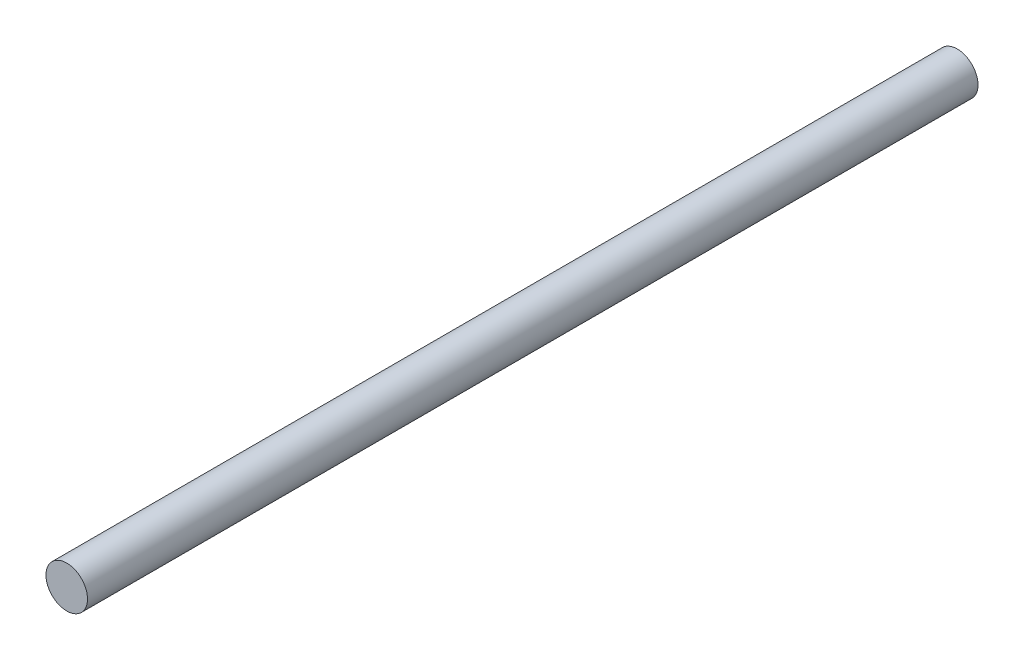
SolidWorks part; units mm, degrees
ref_plane "Front Plane" through (0, 0, 0) normal (0, 0, 1) x (1, 0, 0)
ref_plane "Top Plane" through (0, 0, 0) normal (0, 1, 0) x (1, 0, 0)
ref_plane "Right Plane" through (0, 0, 0) normal (1, 0, 0) x (0, 0, -1)
sketch "Sketch1" plane through (0, 0, 0) normal (0, 0, 1) x (1, 0, 0)
  circle A0 centre (0, 0) radius 0.21
  dimension "D1" = 0.42
extrude "Boss-Extrude1" add sketch "Sketch1" along normal blind 9
